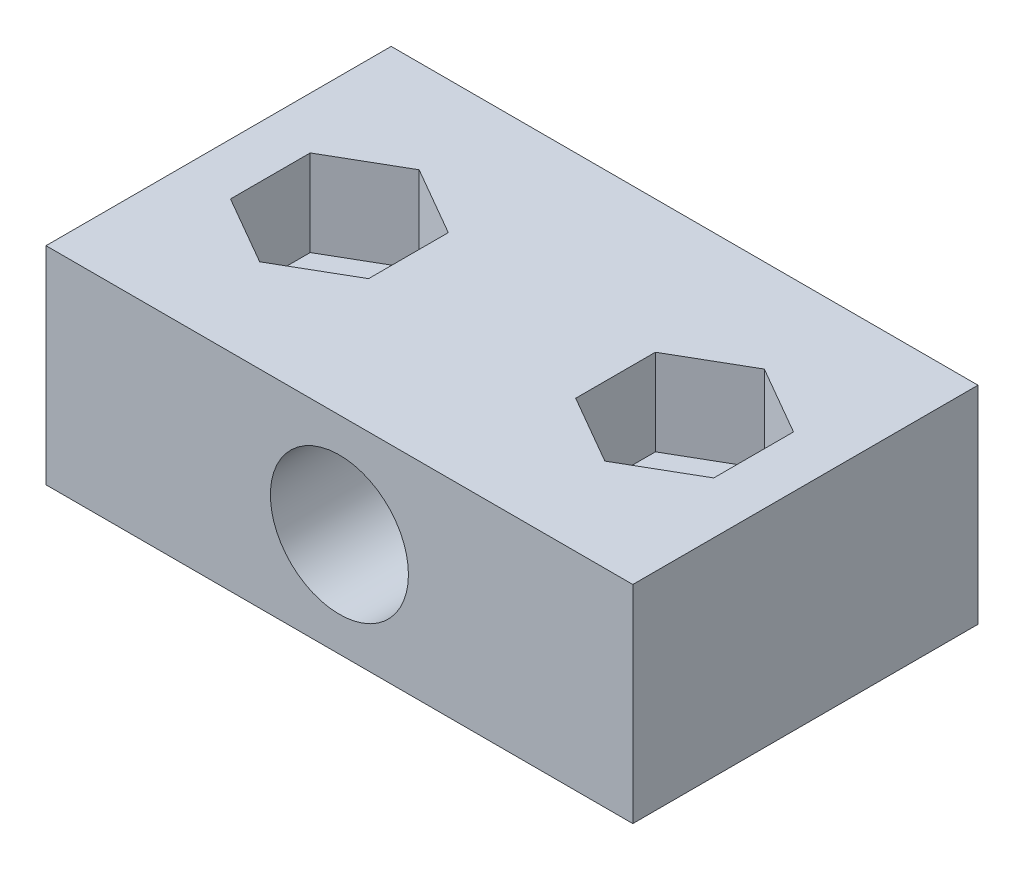
SolidWorks part; units mm, degrees
material "Delrin 2700 NC010, Low Viscosity Acetal Copolymer (SS)"
ref_plane "Front Plane" through (0, 0, 0) normal (0, 0, 1) x (1, 0, 0)
ref_plane "Top Plane" through (0, 0, 0) normal (0, 1, 0) x (1, 0, 0)
ref_plane "Right Plane" through (0, 0, 0) normal (1, 0, 0) x (0, 0, -1)
sketch "Sketch1" plane through (0, 0, 0) normal (0, 0, 1) x (1, 0, 0)
  line L1 (17, -6) -> (-17, -6)
  line L2 (17, -6) -> (17, 6)
  line L3 (17, 6) -> (-17, 6)
  line L4 (-17, -6) -> (-17, 6)
  line L5 (17, -6) -> (-17, 6) construction
  line L6 (17, 6) -> (-17, -6) construction
  point P0 (0, 0)
  dimension "D1" = 12
  dimension "D2" = 34
extrude "Boss-Extrude1" add sketch "Sketch1" along normal blind 20
sketch "Sketch2" plane through (0, 0, 20) normal (0, 0, 1) x (1, 0, 0)
  circle A0 centre (0, 0) radius 4
  dimension "D1" = 8
extrude "Cut-Extrude1" cut sketch "Sketch2" against normal through all
sketch "Sketch3" plane through (0, 6, 0) normal (0, 1, 0) x (1, 0, 0)
  line L0 (-17, -10) -> (0, -10) construction
  line L1 (0, -10) -> (0, 0) construction
  line L2 (-17, -20) -> (-17, 0) construction
  circle A0 centre (-10, -10) radius 2.55
  circle A1 centre (10, -10) radius 2.55
  dimension "D1" = 5.1
  dimension "D2" = 20
extrude "Cut-Extrude2" cut sketch "Sketch3" against normal through all
sketch "Sketch4" plane through (0, 6, 0) normal (0, 1, 0) x (1, 0, 0)
  line L0 (0, 0) -> (0, 6.2689) construction
  line L1 (-10, -5.3812) -> (-14, -7.6906)
  line L2 (-14, -7.6906) -> (-14, -12.3094)
  line L3 (-14, -12.3094) -> (-10, -14.6188)
  line L4 (-10, -14.6188) -> (-6, -12.3094)
  line L5 (-6, -12.3094) -> (-6, -7.6906)
  line L6 (-6, -7.6906) -> (-10, -5.3812)
  line L7 (6, -7.6906) -> (10, -5.3812)
  line L8 (6, -12.3094) -> (6, -7.6906)
  line L9 (10, -14.6188) -> (6, -12.3094)
  line L10 (14, -12.3094) -> (10, -14.6188)
  line L11 (14, -7.6906) -> (14, -12.3094)
  line L12 (10, -5.3812) -> (14, -7.6906)
  circle A0 centre (-10, -10) radius 4 construction
  circle A1 centre (10, -10) radius 4 construction
  dimension "D1" = 8
extrude "Cut-Extrude3" cut sketch "Sketch4" against normal blind 5
sketch "Sketch5" plane through (0, -6, 0) normal (0, -1, 0) x (1, 0, 0)
  circle A0 centre (10, 10) radius 4.5
  circle A1 centre (-10, 10) radius 4.5
  dimension "D1" = 9
extrude "Cut-Extrude4" cut sketch "Sketch5" against normal blind 2
